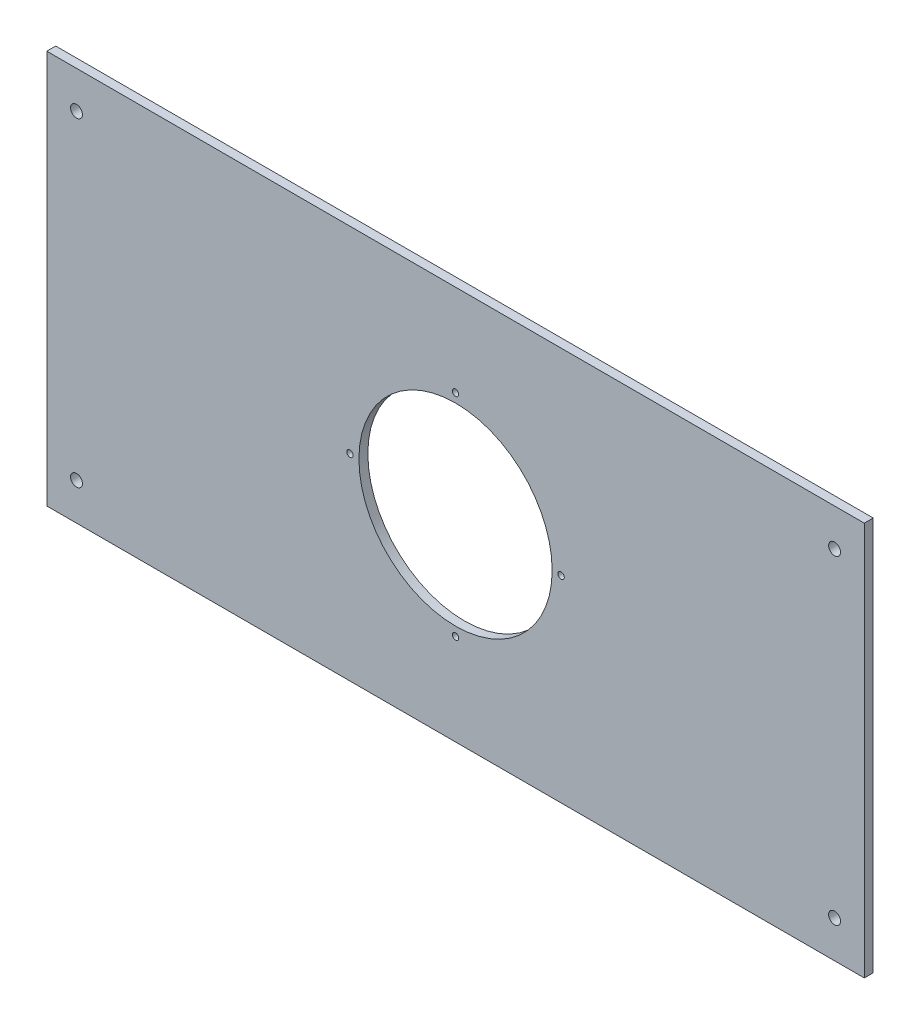
SolidWorks part; units mm, degrees
material "Pin"
ref_plane "Plan de face" through (0, 0, 0) normal (0, 0, 1) x (1, 0, 0)
ref_plane "Plan de dessus" through (0, 0, 0) normal (0, 1, 0) x (1, 0, 0)
ref_plane "Plan de droite" through (0, 0, 0) normal (1, 0, 0) x (0, 0, -1)
sketch "Esquisse1" plane through (0, 0, 0) normal (0, 0, 1) x (1, 0, 0)
  line L1 (-180.6338, 158.5299) -> (369.3662, 158.5299)
  line L2 (-180.6338, 158.5299) -> (-180.6338, -106.4701)
  line L3 (-180.6338, -106.4701) -> (369.3662, -106.4701)
  line L4 (369.3662, 158.5299) -> (369.3662, -106.4701)
  dimension "D1" = 550
  dimension "D2" = 265
extrude "Boss.-Extru.1" add sketch "Esquisse1" along normal blind 6
sketch "Esquisse2" plane through (0, 0, 6) normal (0, 0, 1) x (1, 0, 0)
  line L0 (94.3662, 158.5299) -> (94.3662, -106.4701) construction
  line L1 (369.3662, 158.5299) -> (-180.6338, 158.5299) construction
  line L5 (-180.6338, -106.4701) -> (369.3662, -106.4701) construction
  line L6 (-180.6338, 26.0299) -> (369.3662, 26.0299) construction
  line L7 (-180.6338, 158.5299) -> (-180.6338, -106.4701) construction
  line L8 (369.3662, -106.4701) -> (369.3662, 158.5299) construction
  circle A12 centre (94.3662, 26.0299) radius 65
  circle A13 centre (94.3662, 26.0299) radius 71 construction
  circle A14 centre (94.3662, 97.0299) radius 2.15
  circle A15 centre (165.3662, 26.0299) radius 2.15
  circle A16 centre (94.3662, -44.9701) radius 2.15
  circle A17 centre (23.3662, 26.0299) radius 2.15
  circle A18 centre (-160.6338, 133.5299) radius 4
  circle A19 centre (349.3662, 133.5299) radius 4
  circle A20 centre (349.3662, -81.4701) radius 4
  circle A21 centre (-160.6338, -81.4701) radius 4
  point P26 (94.3662, 26.0299)
  dimension "D1" = 130
  dimension "D2" = 142
  dimension "D5" = 8
  dimension "D3" = 4
  dimension "D4" = 4.3
  dimension "D6" = 20
  dimension "D7" = 25
extrude "Enlèv. mat.-Extru.1" cut sketch "Esquisse2" against normal up to surface (6 mm away) up to face at (94.3662, 26.0299, 0)
